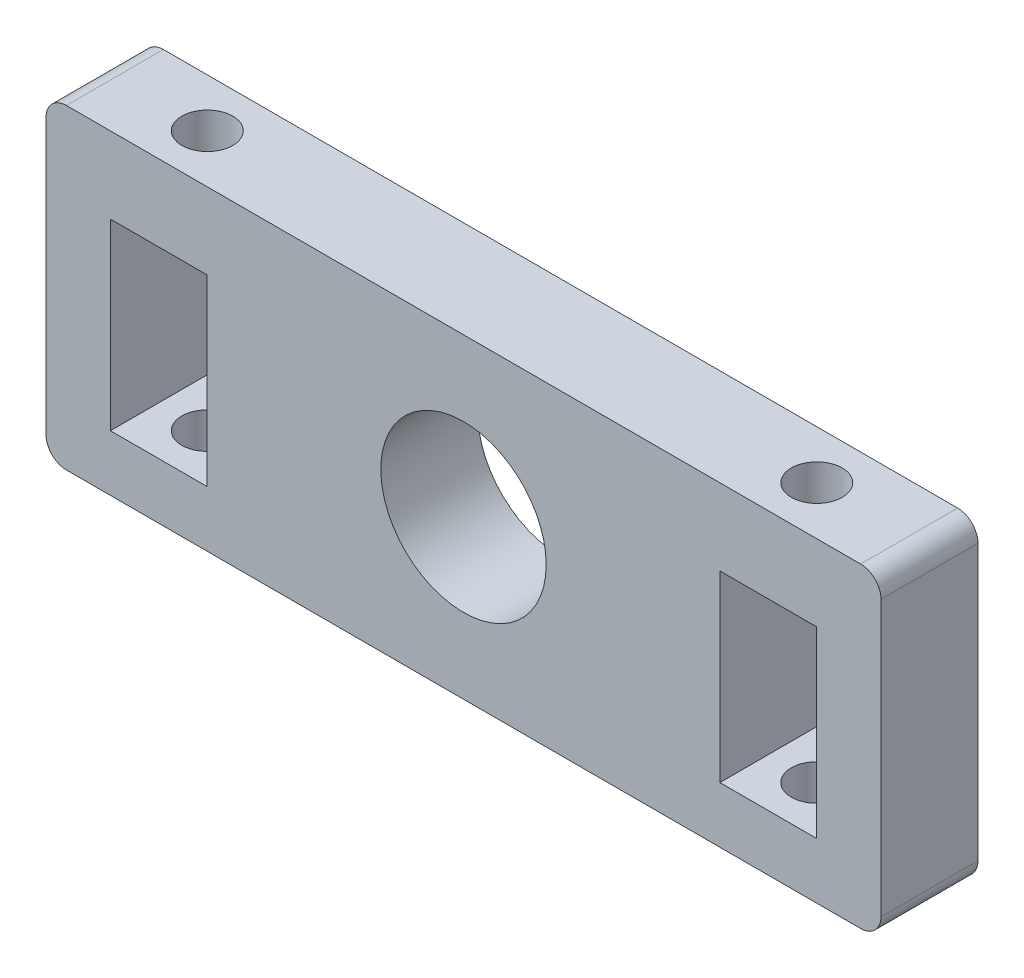
SolidWorks part; units mm, degrees
material "Tuffak AP"
ref_plane "Front Plane" through (0, 0, 0) normal (0, 0, 1) x (1, 0, 0)
ref_plane "Top Plane" through (0, 0, 0) normal (0, 1, 0) x (1, 0, 0)
ref_plane "Right Plane" through (0, 0, 0) normal (1, 0, 0) x (0, 0, -1)
sketch "Sketch1" plane through (0, 0, 0) normal (0, 0, 1) x (1, 0, 0)
  line L0 (0, 31) -> (0, 0) construction
  line L6 (-41, 31) -> (41, 31)
  line L7 (-41, 31) -> (-41, 0)
  line L8 (-41, 0) -> (41, 0)
  line L9 (41, 31) -> (41, 0)
  dimension "D1" = 82
  dimension "D2" = 31
extrude "Boss-Extrude2" add sketch "Sketch1" along normal blind 9.525
fillet "Fillet2" radius 2 4 edges at (-41, 0, 4.7625) (41, 0, 4.7625) (41, 31, 4.7625) (-41, 31, 4.7625)
sketch "Sketch2" plane through (0, 0, 9.525) normal (0, 0, 1) x (1, 0, 0)
  line L0 (-39, 0) -> (39, 0) construction
  circle A0 centre (0, 15.5) radius 8.1198
  dimension "D1" = 15.5
extrude "Cut-Extrude1" cut sketch "Sketch2" against normal through all
sketch "Sketch3" plane through (0, 0, 0) normal (0, 0, -1) x (-1, 0, 0)
  line L5 (-39, 31) -> (39, 31) construction
  line L6 (-34.675, 23.5) -> (-25.175, 23.5)
  line L7 (-34.675, 23.5) -> (-34.675, 5.5)
  line L8 (-34.675, 5.5) -> (-25.175, 5.5)
  line L9 (-25.175, 23.5) -> (-25.175, 5.5)
  line L10 (-41, 2) -> (-41, 29) construction
  dimension "D1" = 7.5
  dimension "D2" = 18
  dimension "D3" = 6.325
  dimension "D4" = 9.5
extrude "Cut-Extrude2" cut sketch "Sketch3" against normal through all
sketch "Sketch5" plane through (0, 31, 0) normal (0, 1, 0) x (1, 0, 0)
  line L0 (-41, -9.525) -> (-41, 0) construction
  line L1 (39, -9.525) -> (-39, -9.525) construction
  circle A0 centre (-29.925, -4.76) radius 2.5
  dimension "D1" = 5
  dimension "D2" = 11.075
  dimension "D3" = 4.765
extrude "Cut-Extrude4" cut sketch "Sketch5" against normal blind 30
mirror "Mirror1" about plane through (0, 0, 0) normal (1, 0, 0) of "Cut-Extrude4", "Cut-Extrude2"
